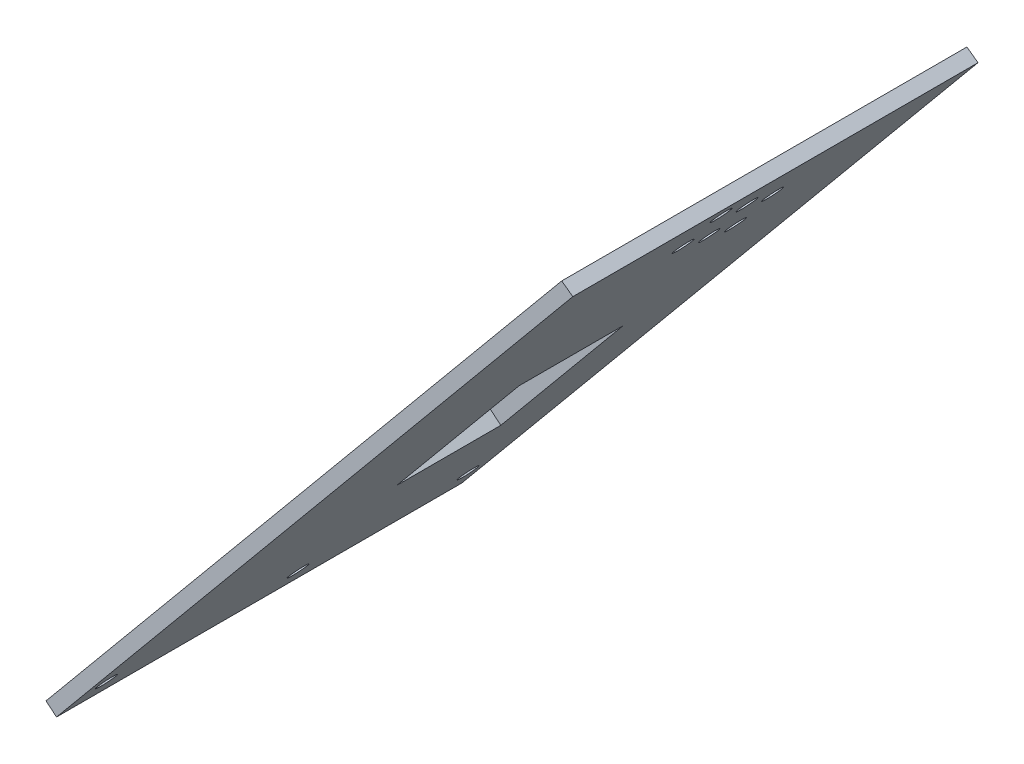
SolidWorks part; units mm, degrees
ref_plane "Piano frontale" through (0, 0, 0) normal (0, 0, 1) x (1, 0, 0)
ref_plane "Piano superiore" through (0, 0, 0) normal (0, 1, 0) x (1, 0, 0)
ref_plane "Piano destro" through (0, 0, 0) normal (1, 0, 0) x (0, 0, -1)
sketch "Schizzo1" plane through (0, 0, 0) normal (0, 0, 1) x (1, 0, 0)
  line L0 (1.3418, 31.372) -> (-14.622, 12.1325)
  line L1 (-14.622, 12.1325) -> (0, 0)
  line L2 (0, 0) -> (92.5902, 111.5888)
  arc A1 (140.9807, 111.5888) -> (92.5902, 111.5888) centre (116.7854, 96.0578) ccw
  dimension "D1" = 19
  dimension "D2" = 25
  dimension "85" = 145
extrude "Estrusione-Sottile1" add sketch "Schizzo1" along normal blind 37 and the other way blind 37 thin
sketch "Schizzo2" plane through (1.9239, -1.5964, 0) normal (0.7696, -0.6386, 0) x (0, 0, -1)
  line L1 (37, 145) -> (-37, 145) construction
  circle A6 centre (-6.5524, 139.8694) radius 1.7
  circle A7 centre (-6.5524, 129.0526) radius 1.7
  circle A8 centre (1.4523, 134.7105) radius 1.7
  circle A9 centre (9.457, 129.5515) radius 1.7
  circle A10 centre (1.5534, 123.8285) radius 1.7
  circle A11 centre (9.6592, 118.6044) radius 1.7
  dimension "D2" = 10.2895
  dimension "D3" = 15.4485
  dimension "D4" = 26.3956
  dimension "D5" = 21.1715
  dimension "D6" = 15.9474
  dimension "D1" = 5.1306
extrude "Taglio-Estrusione2" cut sketch "Schizzo2" against normal blind 23
sketch "Schizzo4" plane through (0, 0, 0) normal (-0.7696, 0.6386, 0) x (0, 0, 1)
  line L0 (-37, 0) -> (37, 0) construction
  line L1 (-17, 40) -> (2, 40)
  line L2 (-17, 40) -> (-17, 75)
  line L3 (-17, 75) -> (2, 75)
  line L4 (2, 40) -> (2, 75)
  line L6 (-37, 0) -> (-37, 145) construction
  line L7 (37, 0) -> (37, 145) construction
  dimension "D1" = 40
  dimension "D2" = 75
  dimension "D3" = 20
  dimension "D4" = 35
extrude "Taglio-Estrusione4" cut sketch "Schizzo4" against normal blind 9
sketch "Schizzo5" plane through (0, 0, 0) normal (-0.7696, 0.6386, 0) x (0, 0, 1)
  circle A0 centre (33, 5.5) radius 1.7
  circle A1 centre (-33, 5.5) radius 1.7
  circle A2 centre (-2, 5.5) radius 1.7
extrude "Taglio-Estrusione5" cut sketch "Schizzo5" against normal blind 9
sketch "Schizzo6" plane through (0, 0, 0) normal (0, 0, 1) x (1, 0, 0)
  line L0 (0, 0) -> (-2.5151, -3.0312)
  line L1 (-2.5151, -3.0312) -> (-24.654, 16.4414)
  line L2 (-24.654, 16.4414) -> (100.0361, 158.2048)
  line L3 (100.0361, 158.2048) -> (192.8252, 76.5907)
  line L4 (192.8252, 76.5907) -> (160.2914, 39.6022)
  line L5 (160.2914, 39.6022) -> (94.6138, 110.1126)
  line L6 (94.6138, 110.1126) -> (92.5902, 111.5888)
  line L7 (92.5902, 111.5888) -> (78.65, 114.8799)
  line L8 (78.65, 114.8799) -> (0, 0)
extrude "Taglio-Estrusione6" cut sketch "Schizzo6" against normal through all both and the other way through all
